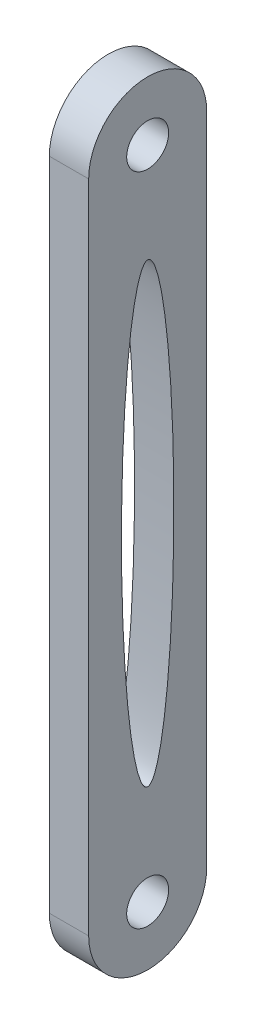
SolidWorks part; units mm, degrees
ref_plane "Front Plane" through (0, 0, 0) normal (0, 0, 1) x (1, 0, 0)
ref_plane "Top Plane" through (0, 0, 0) normal (0, 1, 0) x (1, 0, 0)
ref_plane "Right Plane" through (0, 0, 0) normal (1, 0, 0) x (0, 0, -1)
sketch "Sketch1" plane through (0, 0, 0) normal (1, 0, 0) x (0, 0, -1)
  line L0 (-4.5, 0) -> (-4.5, 50)
  line L1 (4.5, 0) -> (4.5, 50)
  line L2 (0, 0) -> (0, 50) construction
  line L3 (-2, 25) -> (-4.5, 25) construction
  arc A0 (4.5, 0) -> (-4.5, 0) centre (0, 0) cw
  arc A1 (4.5, 50) -> (-4.5, 50) centre (0, 50) ccw
  circle A2 centre (0, 50) radius 1.6
  circle A3 centre (0, 0) radius 1.6
  ellipse E0 centre (0, 25) end of major axis (0, 42.4) minor radius 2
  point P18 (0, 48.4)
  dimension "D1" = 4.5
  dimension "D2" = 3.2
  dimension "D3" = 50
  dimension "D4" = 2.5
  dimension "D5" = 6
extrude "Boss-Extrude1" add sketch "Sketch1" along normal blind 3
